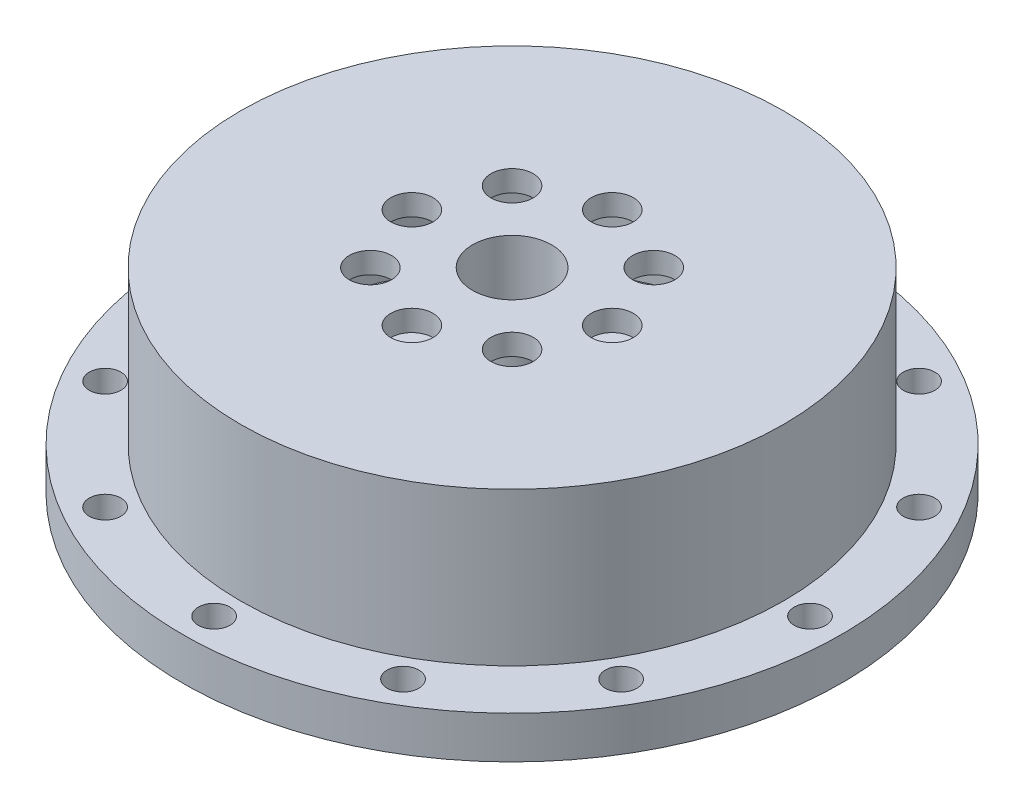
SolidWorks part; units mm, degrees
material "AISI Type 316L stainless steel"
ref_plane "Front Plane" through (0, 0, 0) normal (0, 0, 1) x (1, 0, 0)
ref_plane "Top Plane" through (0, 0, 0) normal (0, 1, 0) x (1, 0, 0)
ref_plane "Right Plane" through (0, 0, 0) normal (1, 0, 0) x (0, 0, -1)
sketch "Sketch1" plane through (0, 0, 0) normal (0, 0, 1) x (1, 0, 0)
  line L0 (0, 0) -> (0, 51.2958) construction
  line L1 (10.5, 32.2161) -> (10.5, 39.2161)
  line L2 (7.5, 32.2161) -> (7.5, 43.2161)
  line L3 (7.5, 43.2161) -> (51.5, 43.2161)
  line L4 (51.5, 43.2161) -> (51.5, 14.2161)
  line L5 (51.5, 14.2161) -> (62.5, 14.2161)
  line L6 (62.5, 14.2161) -> (62.5, 6.2161)
  line L7 (62.5, 6.2161) -> (39, 6.2161)
  line L8 (10, 6.2161) -> (10, 3.2161)
  line L9 (10, 3.2161) -> (7.5, 3.2161)
  line L10 (7.5, 3.2161) -> (7.5, 9.2161)
  line L12 (10.5, 39.2161) -> (48, 39.2161)
  line L13 (48, 39.2161) -> (48, 9.2161)
  line L15 (7.5, 32.2161) -> (10.5, 32.2161)
  line L16 (48, 9.2161) -> (7.5, 9.2161)
  line L20 (36, 6.2161) -> (10, 6.2161)
  line L22 (36, 6.2161) -> (36, 4.2161)
  line L23 (36, 4.2161) -> (39, 4.2161)
  line L24 (39, 6.2161) -> (39, 4.2161)
  dimension "D1" = 40
  dimension "D2" = 15
  dimension "D3" = 3
  dimension "D4" = 8
  dimension "D5" = 125
  dimension "D6" = 11
  dimension "D8" = 15
  dimension "D9" = 2.5
  dimension "D10" = 2
  dimension "D11" = 9
  dimension "D12" = 3
  dimension "D13" = 7
  dimension "D14" = 3.5
  dimension "D7" = 4
revolve "Revolve1" add sketch "Sketch1" angle 360 about L0
sketch "Sketch4" plane through (0, 14.2161, 0) normal (0, 1, 0) x (1, 0, 0)
  circle A0 centre (0, 0) radius 56.5 construction
  circle A1 centre (56.5, 0) radius 3
  circle A9 centre (48.9304, -28.25) radius 3
  circle A10 centre (28.25, -48.9304) radius 3
  circle A11 centre (0, -56.5) radius 3
  circle A12 centre (-28.25, -48.9304) radius 3
  circle A13 centre (-48.9304, -28.25) radius 3
  circle A14 centre (-56.5, 0) radius 3
  circle A15 centre (-48.9304, 28.25) radius 3
  circle A16 centre (-28.25, 48.9304) radius 3
  circle A17 centre (0, 56.5) radius 3
  circle A18 centre (28.25, 48.9304) radius 3
  circle A19 centre (48.9304, 28.25) radius 3
  point P22 (0, 0)
  point P31 (0, 0)
  dimension "D1" = 113
  dimension "D2" = 6
  dimension "D3" = 12
extrude "Cut-Extrude1" cut sketch "Sketch4" against normal blind 10
sketch "Sketch5" plane through (0, 43.2161, 0) normal (0, 1, 0) x (1, 0, 0)
  circle A0 centre (0, 0) radius 19 construction
  circle A1 centre (19, 0) radius 4
  circle A2 centre (13.435, -13.435) radius 4
  circle A3 centre (0, -19) radius 4
  circle A4 centre (-13.435, -13.435) radius 4
  circle A5 centre (-19, 0) radius 4
  circle A6 centre (-13.435, 13.435) radius 4
  circle A7 centre (0, 19) radius 4
  circle A8 centre (13.435, 13.435) radius 4
  point P22 (0, 0)
  dimension "D1" = 8
  dimension "D2" = 38
  dimension "D3" = 8
extrude "Cut-Extrude2" cut sketch "Sketch5" against normal blind 10
sketch "Sketch6" plane through (0, 3.2161, 0) normal (0, -1, 0) x (1, 0, 0)
  line L10 (1, 9) -> (-1, 9)
  line L11 (1, 9) -> (1, 6)
  line L12 (1, 6) -> (-1, 6)
  line L13 (-1, 9) -> (-1, 6)
  circle A0 centre (0, 0) radius 7.5 construction
  point P0 (-7.5, 0)
  point P38 (0, 0)
extrude "Boss-Extrude1" add sketch "Sketch6" against normal up to surface (6 mm away) up to face at (0, 9.2161, -7.5)
